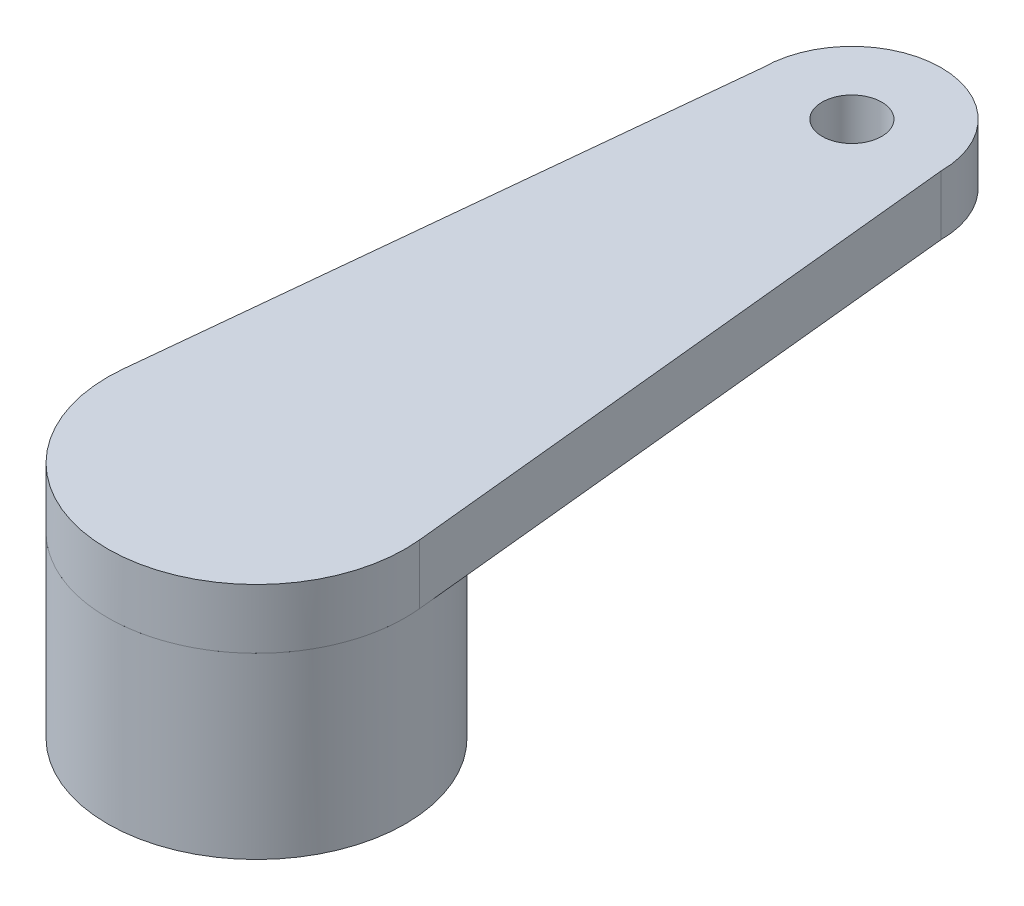
SolidWorks part; units mm, degrees
ref_plane "Front Plane" through (0, 0, 0) normal (0, 0, 1) x (1, 0, 0)
ref_plane "Top Plane" through (0, 0, 0) normal (0, 1, 0) x (1, 0, 0)
ref_plane "Right Plane" through (0, 0, 0) normal (1, 0, 0) x (0, 0, -1)
sketch "Sketch1" plane through (0, 0, 0) normal (0, 1, 0) x (1, 0, 0)
  circle A0 centre (0, 0) radius 1.5
  circle A1 centre (0, 0) radius 2.5
  dimension "D1" = 3
  dimension "D2" = 5
extrude "Boss-Extrude1" add sketch "Sketch1" along normal blind 3
sketch "Sketch3" plane through (0, 3, 0) normal (0, 1, 0) x (1, 0, 0)
  line L0 (-1.5, 10) -> (-2.4872, 0.2519)
  line L1 (1.5, 10) -> (2.4872, 0.2519)
  arc A0 (-2.4872, 0.2519) -> (2.4872, 0.2519) centre (0, 0) ccw
  arc A1 (1.5, 10) -> (-1.5, 10) centre (0, 10) ccw
  circle A2 centre (0, 10) radius 0.5
  dimension "D2" = 3
  dimension "D3" = 1
  dimension "D1" = 10
extrude "Boss-Extrude2" add sketch "Sketch3" along normal blind 1
